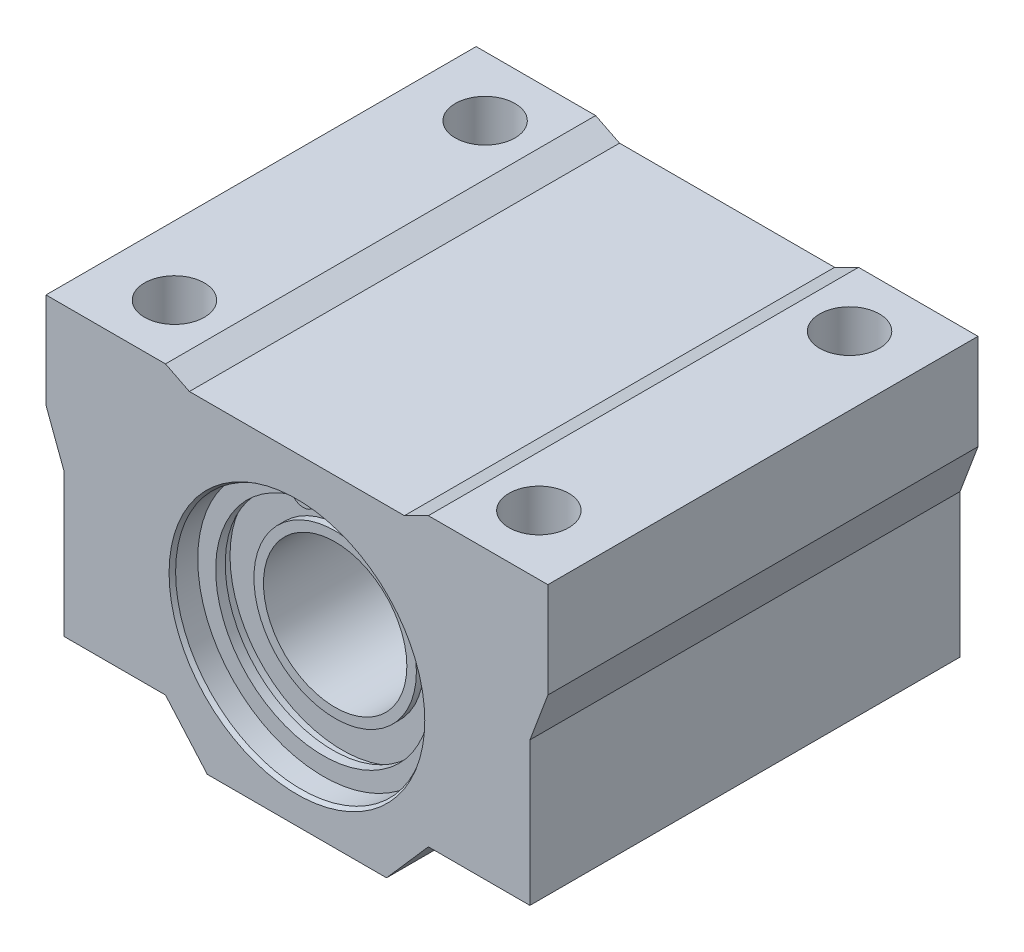
SolidWorks part; units mm, degrees
material "1060 Alloy"
ref_plane "Front Plane" through (0, 0, 0) normal (0, 0, 1) x (1, 0, 0)
ref_plane "Top Plane" through (0, 0, 0) normal (0, 1, 0) x (1, 0, 0)
ref_plane "Right Plane" through (0, 0, 0) normal (1, 0, 0) x (0, 0, -1)
sketch "Sketch1" plane through (0, 0, 0) normal (0, 0, 1) x (1, 0, 0)
  line L0 (0, 0) -> (0, -120.6263) construction
  line L1 (-9, -1) -> (9, -1)
  line L2 (9, -1) -> (11, 0)
  line L3 (11, 0) -> (21, 0)
  line L4 (21, 0) -> (21, -8)
  line L5 (21, -8) -> (19.5, -12)
  line L6 (19.5, -12) -> (19.5, -24)
  line L7 (19.5, -24) -> (11, -24)
  line L8 (11, -24) -> (7.5, -28)
  line L9 (7.5, -28) -> (-7.5, -28)
  line L10 (-19.5, -12) -> (-19.5, -24)
  line L11 (-21, -8) -> (-19.5, -12)
  line L12 (-21, 0) -> (-21, -8)
  line L13 (-11, 0) -> (-21, 0)
  line L14 (-9, -1) -> (-11, 0)
  line L15 (-19.5, -24) -> (-11, -24)
  line L16 (-11, -24) -> (-7.5, -28)
  circle A0 centre (0, -15) radius 10.5
  point P19 (0, -1)
  point P21 (0, -28)
  dimension "D4" = 21
  dimension "D1" = 8
  dimension "D2" = 1
  dimension "D3" = 1.5
  dimension "D5" = 42
  dimension "D6" = 28
  dimension "D7" = 12
  dimension "D8" = 2
  dimension "D9" = 24
  dimension "D10" = 15
  dimension "D11" = 10
  dimension "D12" = 15
  dimension "D13" = 22
extrude "Boss-Extrude1" add sketch "Sketch1" along normal mid plane 36
sketch "Sketch2" plane through (0, 0, 0) normal (1, 0, 0) x (0, 0, -1)
  line L0 (-30.2753, -15) -> (18, -15) construction
  line L1 (18, -25.5) -> (18, -4.5) construction
  line L2 (18, -25.5) -> (18, -4.5) construction
  line L3 (0, 0) -> (0, -32.2949) construction
  line L4 (-15, -4.5) -> (15, -4.5)
  line L5 (15, -4.5) -> (15, -5.6)
  line L6 (15, -5.6) -> (14.2, -5.6)
  line L7 (14.2, -5.6) -> (14.2, -8.2)
  line L8 (14.2, -8.2) -> (14.8, -8.2)
  line L9 (14.8, -8.2) -> (14.8, -9)
  line L10 (14.8, -9) -> (-14.8, -9)
  line L11 (-14.8, -8.2) -> (-14.8, -9)
  line L12 (-14.2, -8.2) -> (-14.8, -8.2)
  line L13 (-14.2, -5.6) -> (-14.2, -8.2)
  line L14 (-15, -5.6) -> (-14.2, -5.6)
  line L15 (-15, -4.5) -> (-15, -5.6)
  line L16 (14.8, -21) -> (-14.8, -21) construction
  line L17 (-15, -25.5) -> (15, -25.5) construction
  point P16 (0, -9)
  point P21 (0, -4.5)
  dimension "D1" = 1.1
  dimension "D2" = 0.8
  dimension "D3" = 21
  dimension "D4" = 12
  dimension "D5" = 30
  dimension "D6" = 0.8
  dimension "D7" = 0.6
revolve "Revolve1" add sketch "Sketch2" angle 360 about L0
sketch "Sketch3" plane through (0, 0, 15) normal (0, 0, 1) x (1, 0, 0)
  line L0 (0, 4.2304) -> (0, -35.7092) construction
  line L1 (1.1412, -4.0594) -> (0.6431, -5.3567)
  line L2 (-1.1412, -4.0594) -> (-0.6431, -5.3567)
  circle A0 centre (1.6627, -5.7482) radius 0.4873
  circle A1 centre (0, -15) radius 9.4 construction
  arc A2 (0.6431, -5.3567) -> (2.5594, -6.3716) centre (1.6627, -5.7482) ccw
  arc A3 (1.1412, -4.0594) -> (-1.1412, -4.0594) centre (0, -15) cw
  arc A4 (2.5594, -6.3716) -> (-2.5594, -6.3716) centre (0, -15) cw
  circle A5 centre (-1.6627, -5.7482) radius 0.4873
  arc A6 (-0.6431, -5.3567) -> (-2.5594, -6.3716) centre (-1.6627, -5.7482) cw
  point P14 (0, -15.2009)
  dimension "D1" = 11
  dimension "D3" = 9
extrude "Boss-Extrude2" add sketch "Sketch3" along normal blind 0.8
mirror "Mirror1" about plane through (0, 0, 0) normal (0, 0, 1) of "Boss-Extrude2"
hole_wizard "M5 Tapped Hole1" positions "Sketch5" profile "Sketch6" tap size "M5" standard "DIN" end condition through all
sketch "Sketch5" plane through (0, 0, 0) normal (0, 1, 0) x (1, 0, 0)
  line L0 (0, 19.7581) -> (0, 0) construction
  line L1 (0, 0) -> (23.7777, 0) construction
  point P6 (15.25, 13)
  point P10 (15.25, -13)
  point P12 (-15.25, 13)
  point P13 (-15.25, -13)
  dimension "D1" = 30.5
  dimension "D2" = 26
sketch "Sketch6" plane through (15.25, 0, -13) normal (1, 0, 0) x (0, 0, 1)
  line L0 (0, 0) -> (0, 24)
  line L1 (2.1, 23.6) -> (2.5, 24)
  line L2 (2.1, 23.6) -> (2.1, 12)
  line L3 (2.1, 12) -> (2.5, 12)
  line L4 (2.5, 12) -> (2.5, 0)
  line L5 (2.5, 0) -> (0, 0)
  line L11 (0, -6.35) -> (0, 107.95) construction
  line L12 (2.5, 24) -> (0, 24)
  line L13 (-2.1, 23.6) -> (-2.5, 24) construction
  dimension "Thru Tap Drill Dia." = 4.2
  dimension "Thru Tap Drill Depth" = 24
  dimension "Thread Major Dia." = 5
  dimension "Thread Depth" = 12
  dimension "Far C'Sink Dia." = 5
  dimension "Far C'Sink Angle" = 90
chamfer "Chamfer1" distance 0.2 angle 60 2 edges at (10.5, -15, -18) (10.5, -15, 18)
